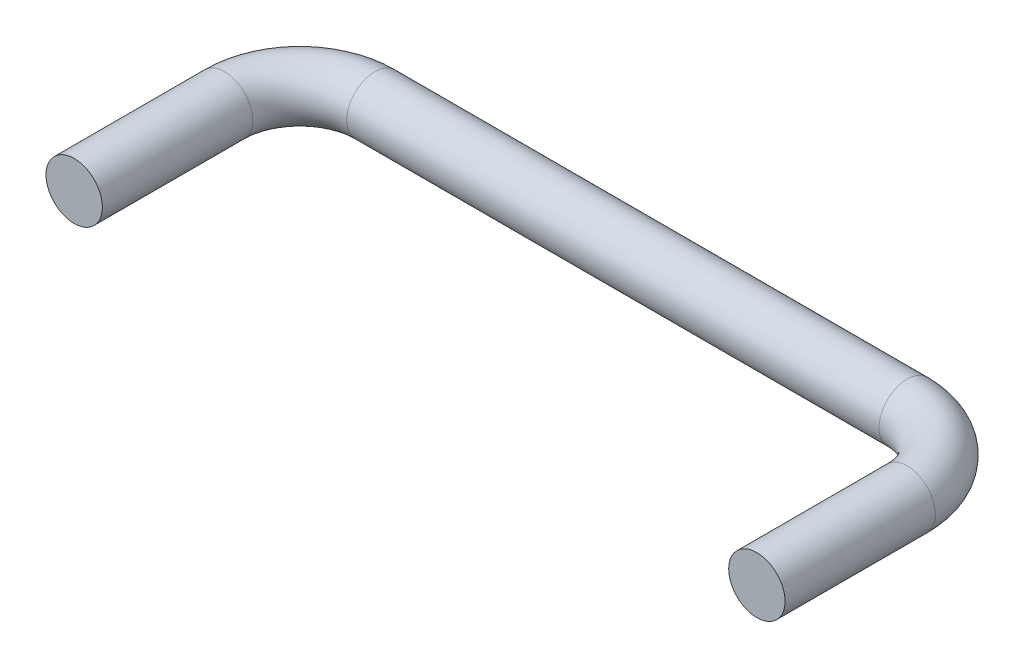
SolidWorks part; units mm, degrees
material "1.4006 (X10Cr13)"
ref_plane "Alzado" through (0, 0, 0) normal (0, 0, 1) x (1, 0, 0)
ref_plane "Planta" through (0, 0, 0) normal (0, 1, 0) x (1, 0, 0)
ref_plane "Vista lateral" through (0, 0, 0) normal (1, 0, 0) x (0, 0, -1)
sketch "Croquis1" plane through (0, 0, 0) normal (0, 1, 0) x (1, 0, 0)
  line L0 (0, 0) -> (0, 20)
  line L1 (10, 30) -> (80.824, 30)
  line L2 (90.824, 20) -> (90.824, 0)
  arc A0 (80.824, 30) -> (90.824, 20) centre (80.824, 20) cw
  arc A1 (10, 30) -> (0, 20) centre (10, 20) ccw
  point P8 (90.824, 30)
  point P11 (0, 30)
  dimension "D3" = 10
  dimension "D1" = 30
  dimension "D2" = 90.824
sketch "Croquis2" plane through (0, 0, 0) normal (0, 0, 1) x (1, 0, 0)
  circle A0 centre (0, 0) radius 3.75
  dimension "D1" = 7.5
sweep "Barrer1" add profiles "Croquis2" path "Croquis1"
